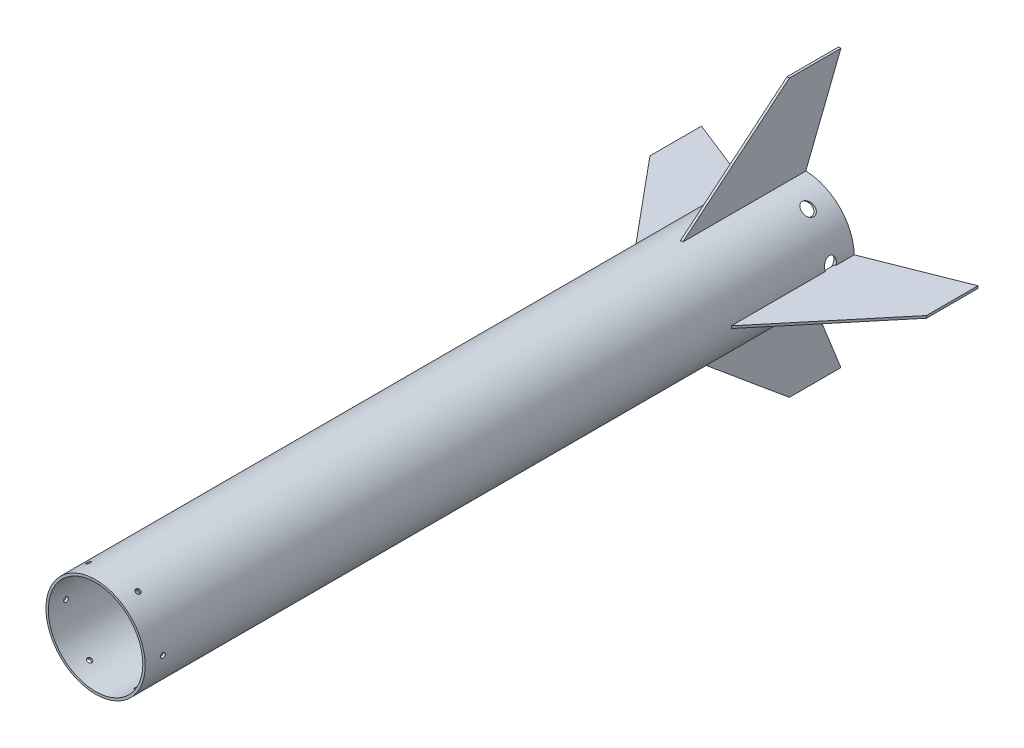
SolidWorks part; units mm, degrees
material "E-Glass Fiber"
ref_plane "Front Plane" through (0, 0, 0) normal (0, 0, 1) x (1, 0, 0)
ref_plane "Top Plane" through (0, 0, 0) normal (0, 1, 0) x (1, 0, 0)
ref_plane "Right Plane" through (0, 0, 0) normal (1, 0, 0) x (0, 0, -1)
sketch "Sketch1" plane through (0, 0, 0) normal (0, 0, 1) x (1, 0, 0)
  circle A0 centre (0, 0) radius 42
  circle A1 centre (0, 0) radius 40
  dimension "D1" = 84
  dimension "D2" = 2
extrude "Boss-Extrude1" add sketch "Sketch1" along normal blind 600
ref_plane "Bolts to Avionics" through (45, 0, 0) normal (1, 0, 0) x (0, 0, -1)
sketch "Sketch2" plane through (45, 0, 0) normal (1, 0, 0) x (0, 0, -1)
  line L0 (-600, 0) -> (-585, 0) construction
  line L1 (-600, 42) -> (-600, -42) construction
  circle A0 centre (-585, 0) radius 2
  dimension "D2" = 4
  dimension "D1" = 15
extrude "Cut-Extrude1" cut sketch "Sketch2" against normal up to surface (5 mm away) up to face at (40, 0, 600)
pattern_circular "CirPattern1" count 6 over 360 about axis through (0, 0, 600) along (0, 0, -1) of "Cut-Extrude1"
ref_plane "Tail bolts" through (-42, 0, 0) normal (-1, 0, 0) x (0, 0, 1)
sketch "Sketch4" plane through (-42, 0, 0) normal (-1, 0, 0) x (0, 0, 1)
  line L0 (0, -21.5736) -> (20, -21.5736) construction
  line L1 (0, 42) -> (0, -42) construction
  circle A0 centre (20, -21.5736) radius 5
  dimension "D2" = 10
  dimension "D1" = 20
extrude "Cut-Extrude2" cut sketch "Sketch4" against normal up to surface (8.3165 mm away) contours A0
pattern_circular "CirPattern2" count 7 over 360 about axis through (0, 0, 600) along (0, 0, -1) of "Cut-Extrude2"
sketch "Tail Configuration" plane through (0, 0, 0) normal (0, 0, -1) x (-1, 0, 0)
  line L0 (0, 0) -> (0, 42) construction
  line L1 (0, 0) -> (36.3731, -21) construction
  line L2 (0, 0) -> (-36.3731, -21) construction
  line L3 (31.4856, -29.4654) -> (41.2605, -12.5346) construction
  line L4 (-41.8479, -11.5173) -> (-30.8983, -30.4827) construction
  circle A0 centre (0, 0) radius 42 construction
  point P10 (0, 0)
  point P12 (36.3731, -21)
  point P15 (-36.3731, -21)
  dimension "D1" = 3
ref_plane "Fin 1" through (0, 42, 0) normal (0, 1, 0) x (1, 0, 0)
sketch "Sketch6" plane through (0, 42, 0) normal (0, 1, 0) x (1, 0, 0)
  line L4 (0, 0) -> (0, -62.2364) construction
  point P4 (0, 0)
ref_plane "Plane6" through (0, 0, 0) normal (-1, 0, 0) x (0, 0, 1)
sketch "Sketch13" plane through (0, 0, 0) normal (-1, 0, 0) x (0, 0, 1)
  line L0 (0, 42) -> (104, 42) construction
  line L1 (52.1788, 42) -> (-52.1788, 42) construction
  line L2 (104, 42) -> (13.9, 117)
  line L3 (13.9, 117) -> (-29.7, 117)
  line L4 (-29.7, 117) -> (0, 42)
  line L5 (0, 42) -> (0, 117) construction
  line L6 (78, 42) -> (78, 50.3814) construction
  line L7 (78, 42) -> (3, 117) construction
  line L9 (0, 42) -> (104, 42) construction
  line L10 (0, 42) -> (0, 41)
  line L11 (0, 41) -> (104, 41)
  line L12 (104, 42) -> (104, 41)
  dimension "D5" = 26
  dimension "D6" = 10.9
  dimension "D7" = 1
  dimension "D1" = 75
  dimension "D2" = 104
  dimension "D3" = 43.6
  dimension "D4" = 45
extrude "Boss-Extrude6" add sketch "Sketch13" along normal mid plane 2 separate body
ref_plane "Fin 2" [suppressed] through (-36.3731, -21, 0) normal (0.866, 0.5, 0) x (-0.5, 0.866, 0)
sketch "Sketch9" [suppressed] plane through (-36.3731, -21, 0) normal (0.866, 0.5, 0) x (-0.5, 0.866, 0)
  line L0 (0, 0) -> (0, 21.8091) construction
ref_plane "Plane4" [suppressed] through (0, 0, 0) normal (-0.5, 0.866, 0) x (0, 0, 1)
sketch "Sketch10" [suppressed] plane through (0, 0, 0) normal (-0.5, 0.866, 0) x (0, 0, 1)
  line L0 (0, -42) -> (-10.3999, -117)
  line L1 (-10.3999, -117) -> (33.2001, -117)
  line L2 (33.2001, -117) -> (104, -42)
  line L3 (24.967, -42) -> (600, -42) construction
  line L4 (104, -42) -> (0, -42) construction
  line L5 (78, -42) -> (78, -62.2562) construction
  line L6 (78, -42) -> (22.3001, -117) construction
  line L7 (0, -42) -> (0, -117) construction
  line L9 (0, -42) -> (104, -42) construction
  line L10 (0, -42) -> (0, -41)
  line L11 (0, -41) -> (104, -41)
  line L12 (104, -42) -> (104, -41)
  dimension "D1" = 104
  dimension "D3" = 45
  dimension "D4" = 75
  dimension "D2" = 43.6
  dimension "D5" = 26
  dimension "D6" = 10.9
  dimension "D7" = 1
extrude "Boss-Extrude7" [suppressed] add sketch "Sketch10" along normal mid plane 2
ref_plane "Fin 3" [suppressed] through (36.3731, -21, 0) normal (-0.866, 0.5, 0) x (-0.5, -0.866, 0)
sketch "Sketch11" [suppressed] plane through (36.3731, -21, 0) normal (-0.866, 0.5, 0) x (-0.5, -0.866, 0)
  line L0 (0, 0) -> (0, 29.9322) construction
ref_plane "Plane5" [suppressed] through (0, 0, 0) normal (-0.5, -0.866, 0) x (0, 0, 1)
sketch "Sketch12" [suppressed] plane through (0, 0, 0) normal (-0.5, -0.866, 0) x (0, 0, 1)
  line L0 (0, -42) -> (104, -42) construction
  line L1 (0, -42) -> (600, -42) construction
  line L2 (104, -42) -> (33.2001, -117)
  line L3 (33.2001, -117) -> (-10.3999, -117)
  line L4 (-10.3999, -117) -> (0, -42)
  line L5 (0, -42) -> (0, -117) construction
  line L6 (78, -42) -> (78, -53.3564) construction
  line L7 (78, -42) -> (22.3001, -117) construction
  line L9 (0, -42) -> (104, -42) construction
  line L10 (0, -42) -> (0, -41)
  line L11 (0, -41) -> (104, -41)
  line L12 (104, -42) -> (104, -41)
  dimension "D1" = 104
  dimension "D3" = 45
  dimension "D5" = 26
  dimension "D7" = 1
  dimension "D2" = 75
  dimension "D4" = 10.9
  dimension "D6" = 43.6
extrude "Boss-Extrude5" [suppressed] add sketch "Sketch12" along normal mid plane 2
pattern_circular "CirPattern3" count 4 over 360 about axis through (0, 0, 0) along (0, 0, 1) of "Boss-Extrude6"
fillet "Fillet5" [suppressed] radius 1
equation "\"Tip Chord\"= 43.6mm"
equation "\"Root Chord\"= 104mm"
equation "\"Height\"= 75mm"
equation "\"Sweep angle\"= 45deg"
equation "\"D1@Sketch10\"=\"Root Chord\""
equation "\"D3@Sketch10\"=\"Sweep angle\""
equation "\"D4@Sketch10\"=\"Height\""
equation "\"D2@Sketch10\"=\"Tip Chord\""
equation "\"D1@Sketch12\"=\"Root Chord\""
equation "\"D2@Sketch12\"=\"Height\""
equation "\"D3@Sketch12\"=\"Sweep angle\""
equation "\"D4@Sketch12\"=\"Tip Chord\"/4"
equation "\"D5@Sketch12\"=\"Root Chord\"/4"
equation "\"D6@Sketch12\"=\"Tip Chord\""
equation "\"D5@Sketch10\"=\"Root Chord\"/4"
equation "\"D6@Sketch10\"=\"Tip Chord\"/4"
equation "\"D1@Sketch13\"=\"Height\""
equation "\"D2@Sketch13\"=\"Root Chord\""
equation "\"D3@Sketch13\"=\"Tip Chord\""
equation "\"D4@Sketch13\"=\"Sweep angle\""
equation "\"D5@Sketch13\"=\"Root Chord\"/4"
equation "\"D6@Sketch13\"=\"Tip Chord\"/4"
